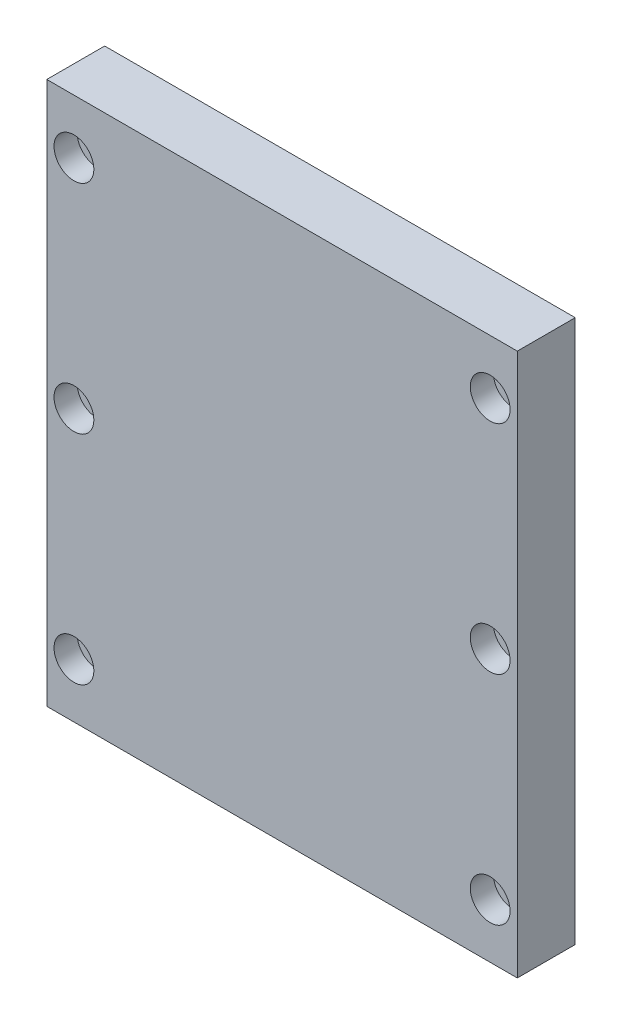
SolidWorks part; units mm, degrees
material "Простая углеродистая сталь"
ref_plane "Front" through (0, 0, 0) normal (0, 0, 1) x (1, 0, 0)
ref_plane "Top" through (0, 0, 0) normal (0, 1, 0) x (1, 0, 0)
ref_plane "Right" through (0, 0, 0) normal (1, 0, 0) x (0, 0, -1)
sketch "Sketch1" plane through (0, 0, 0) normal (0, 0, 1) x (1, 0, 0)
  line L1 (-65, 75) -> (65, 75)
  line L2 (-65, 75) -> (-65, -75)
  line L3 (-65, -75) -> (65, -75)
  line L4 (65, 75) -> (65, -75)
  line L5 (-65, 75) -> (65, -75) construction
  line L6 (-65, -75) -> (65, 75) construction
  point P0 (0, 0)
  dimension "D1" = 150
  dimension "D2" = 130
extrude "Extrude1" add sketch "Sketch1" along normal blind 16
hole_wizard "CBORE for M6 Hex Socket Head Cap Screw1" positions "Sketch2" profile "Sketch3" counterbore size "M6" standard "DIN" end condition through all
sketch "Sketch2" plane through (0, 0, 16) normal (0, 0, 1) x (1, 0, 0)
  line L0 (-65, 75) -> (-65, -75) construction
  line L1 (0, 0) -> (0, 18.455) construction
  point P0 (-57.5, 60)
  point P2 (-57.5, 0)
  point P4 (-57.5, -60)
  point P17 (57.5, -60)
  point P18 (57.5, 0)
  point P19 (57.5, 60)
  dimension "D1" = 7.5
  dimension "D2" = 60
  dimension "D3" = 60
sketch "Sketch3" plane through (-57.5, 60, 16) normal (1, 0, 0) x (0, -1, 0)
  line L0 (0, 0) -> (0, 16)
  line L1 (0, 16) -> (3.3, 16)
  line L3 (3.3, 16) -> (3.3, 6.4)
  line L4 (3.3, 6.4) -> (5.5, 6.4)
  line L5 (5.5, 6.4) -> (5.5, 0)
  line L7 (5.5, 0) -> (0, 0)
  line L11 (0, -6.35) -> (0, 107.95) construction
  dimension "Диаметр сквозного отверстия" = 6.6
  dimension "Глубина сквозного отверстия" = 16
  dimension "Диаметр цековки" = 11
  dimension "Глубина цековки" = 6.4
